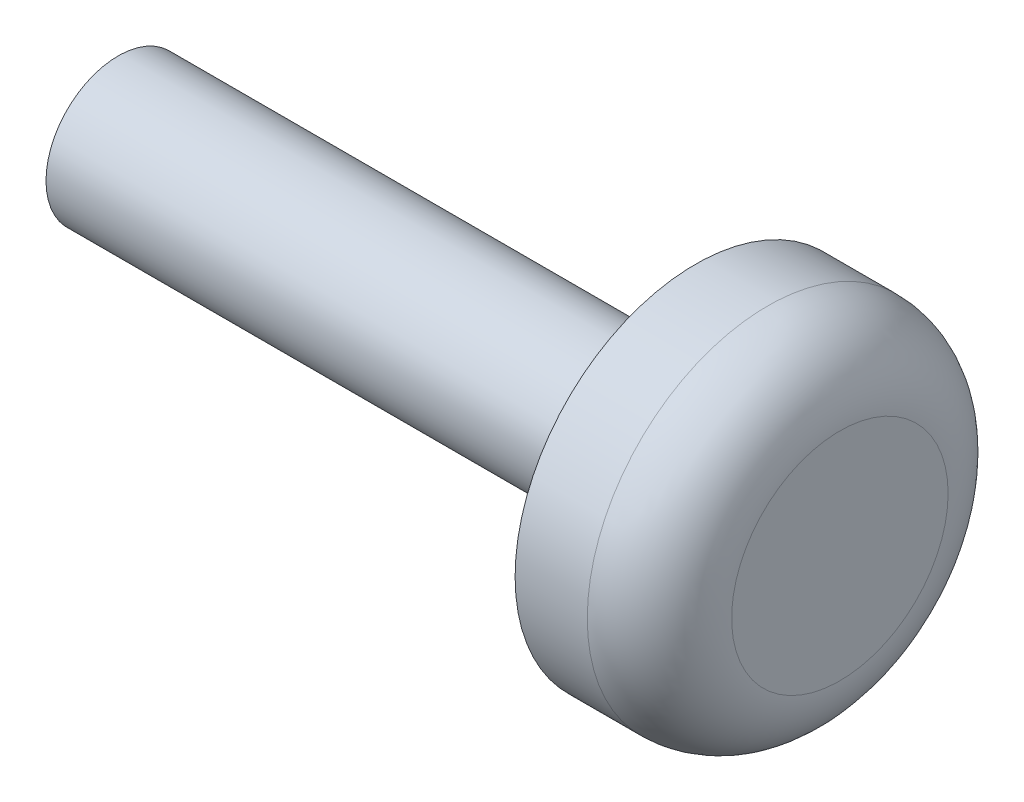
SolidWorks part; units mm, degrees
ref_plane "Ebene vorne" through (0, 0, 0) normal (0, 0, 1) x (1, 0, 0)
ref_plane "Ebene oben" through (0, 0, 0) normal (0, 1, 0) x (1, 0, 0)
ref_plane "Ebene rechts" through (0, 0, 0) normal (1, 0, 0) x (0, 0, -1)
sketch "Skizze1" plane through (0, 0, 0) normal (1, 0, 0) x (0, 0, -1)
  circle A0 centre (0, 0) radius 2.5
  dimension "D1" = 5
extrude "Aufsatz-Linear austragen1" add sketch "Skizze1" along normal blind 2
sketch "Skizze2" plane through (0, 0, 0) normal (-1, 0, 0) x (0, 0, 1)
  circle A0 centre (0, 0) radius 1
  dimension "D1" = 2
extrude "Aufsatz-Linear austragen2" add sketch "Skizze2" along normal blind 8
fillet "Verrundung1" radius 1 1 edges at (2, 0, -2.5)
